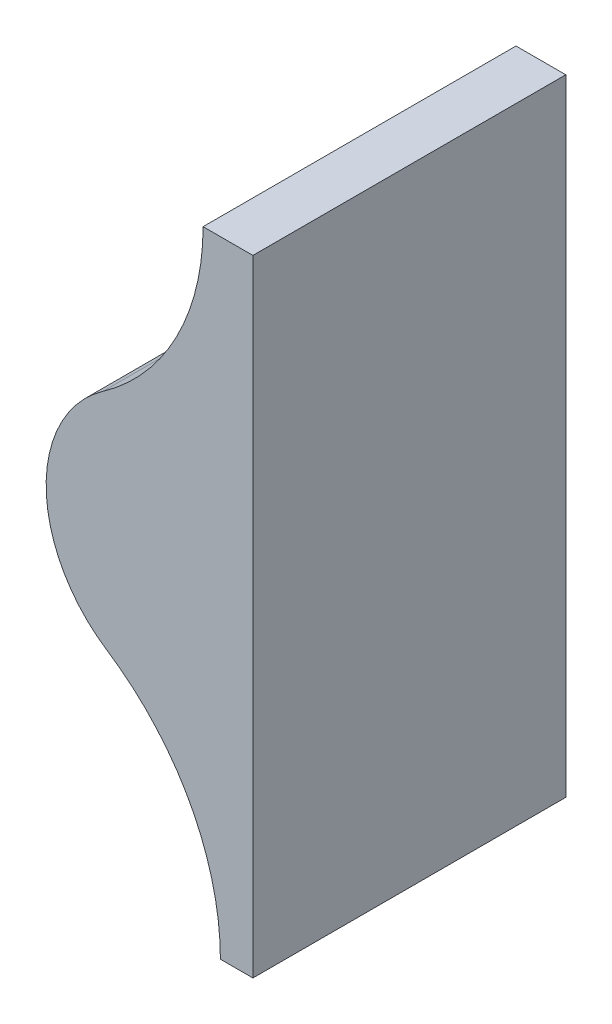
SolidWorks part; units mm, degrees
ref_plane "Front Plane" through (0, 0, 0) normal (0, 0, 1) x (1, 0, 0)
ref_plane "Top Plane" through (0, 0, 0) normal (0, 1, 0) x (1, 0, 0)
ref_plane "Right Plane" through (0, 0, 0) normal (1, 0, 0) x (0, 0, -1)
sketch "Sketch1" plane through (0, 0, 0) normal (0, 0, 1) x (1, 0, 0)
  line L0 (0, 0) -> (0, 152.4)
  line L1 (0, 152.4) -> (-12.1297, 152.4)
  line L2 (-7.9141, 0) -> (0, 0)
  line L3 (-7.9141, 0) -> (-7.9141, -31.1208) construction
  line L4 (-12.1297, 152.4) -> (-12.1297, 163.9835) construction
  arc A0 (-12.1297, 152.4) -> (-36.459, 105.5195) centre (-69.4616, 152.4) cw
  arc A1 (-36.459, 105.5195) -> (-35.6164, 51.4063) centre (-17.6138, 78.7498) ccw
  arc A2 (-35.6164, 51.4063) -> (-7.9141, 0) centre (-69.4616, 0) cw
  dimension "D2" = 61.5475
  dimension "D1" = 152.4
extrude "Boss-Extrude1" add sketch "Sketch1" along normal blind 76.2
